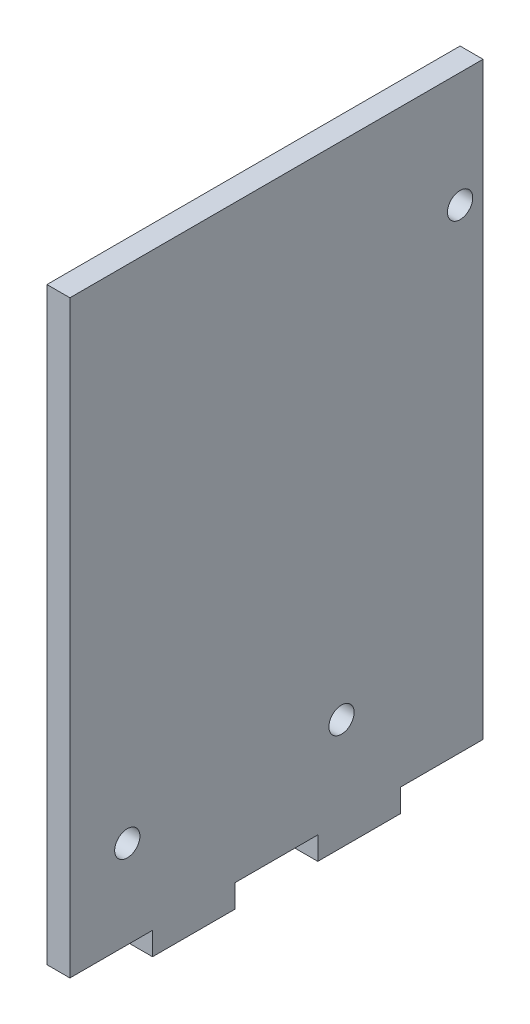
SolidWorks part; units mm, degrees
ref_plane "Ön Düzlem" through (0, 0, 0) normal (0, 0, 1) x (1, 0, 0)
ref_plane "Üst Düzlem" through (0, 0, 0) normal (0, 1, 0) x (1, 0, 0)
ref_plane "Sağ Düzlem" through (0, 0, 0) normal (1, 0, 0) x (0, 0, -1)
sketch "Sketch1" plane through (0, 0, 0) normal (1, 0, 0) x (0, 0, -1)
  line L1 (16.2, -40) -> (5.4, -40)
  line L2 (27, -37) -> (27, 40)
  line L4 (-27, -37) -> (-27, 40)
  line L5 (24.975, -37) -> (-27, 40) construction
  line L6 (27, 40) -> (-24.975, -37) construction
  line L7 (-16.2, -40) -> (-5.4, -40)
  line L9 (5.4, -40) -> (16.2, -40)
  line L12 (-27, -37) -> (-16.2, -37)
  line L13 (16.2, -40) -> (16.2, -37)
  line L14 (5.4, -40) -> (5.4, -37)
  line L15 (-5.4, -40) -> (-5.4, -37)
  line L16 (-16.2, -40) -> (-16.2, -37)
  line L17 (-5.4, -37) -> (5.4, -37)
  line L18 (16.2, -37) -> (27, -37)
  line L19 (-5.4, -40) -> (-16.2, -40)
  line L20 (-27, 40) -> (27, 40)
  circle A0 centre (24, 25) radius 1.65
  circle A1 centre (-19.5, -25.5) radius 1.65
  circle A2 centre (8.5, -25.5) radius 1.65
  point P0 (0, 0)
extrude "Boss-Extrude1" add sketch "Sketch1" along normal blind 3 contours L20 L4 L12 L16 L7 L15 L17 L14 L1 L13 L18 L2 A2 A1 A0
